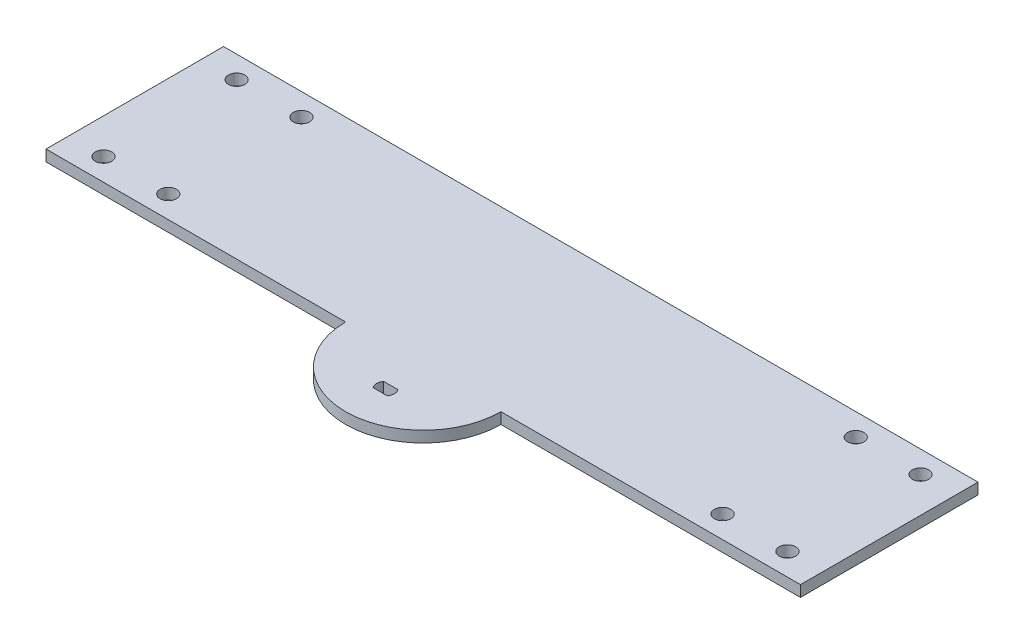
SolidWorks part; units mm, degrees
ref_plane "Front Plane" through (0, 0, 0) normal (0, 0, 1) x (1, 0, 0)
ref_plane "Top Plane" through (0, 0, 0) normal (0, 1, 0) x (1, 0, 0)
ref_plane "Right Plane" through (0, 0, 0) normal (1, 0, 0) x (0, 0, -1)
sketch "Sketch1" plane through (0, 0, 0) normal (0, 1, 0) x (1, 0, 0)
  line L0 (-2.032, 1.524) -> (2.032, 1.524)
  line L1 (-2.032, -1.524) -> (2.032, -1.524)
  line L2 (0, 0) -> (0, -11.43) construction
  line L3 (-107.95, 61.595) -> (107.95, 61.595)
  line L4 (-107.95, 61.595) -> (-107.95, 10.795)
  line L5 (-107.95, 10.795) -> (-22.225, 10.795)
  line L6 (107.95, 61.595) -> (107.95, 10.795)
  line L7 (-107.95, 61.595) -> (107.95, 10.795) construction
  line L8 (-107.95, 10.795) -> (107.95, 61.595) construction
  line L9 (22.225, 10.795) -> (107.95, 10.795)
  arc A0 (-2.032, 1.524) -> (-2.032, -1.524) centre (0, 0) ccw
  arc A1 (2.032, -1.524) -> (2.032, 1.524) centre (0, 0) ccw
  arc A2 (-22.225, 10.795) -> (22.225, 10.795) centre (0, 10.795) ccw
  point P8 (0, 36.195)
  dimension "D1" = 5.08
  dimension "D3" = 44.45
  dimension "D2" = 3.048
  dimension "D4" = 50.8
  dimension "D5" = 215.9
  dimension "D6" = 11.43
extrude "Boss-Extrude1" add sketch "Sketch1" along normal blind 3.175
sketch "Sketch2" plane through (0, 3.175, 0) normal (0, 1, 0) x (1, 0, 0)
  line L0 (-107.95, 55.245) -> (-97.8535, 55.245) construction
  line L1 (-107.95, 61.595) -> (-107.95, 10.795) construction
  line L2 (-97.8535, 10.795) -> (-97.8535, 14.7955) construction
  line L3 (107.95, 61.595) -> (-107.95, 61.595) construction
  line L4 (-107.95, 10.795) -> (-22.225, 10.795) construction
  line L6 (0, 0) -> (0, 61.595) construction
  line L9 (107.95, 55.245) -> (97.8535, 55.245) construction
  line L11 (-97.8535, 57.5945) -> (-97.8535, 61.595) construction
  circle A0 centre (-97.8535, 55.245) radius 2.3495
  circle A1 centre (-97.8535, 17.145) radius 2.3495
  circle A2 centre (-79.3115, 17.145) radius 2.3495
  circle A3 centre (-79.3115, 55.245) radius 2.3495
  circle A4 centre (79.3115, 55.245) radius 2.3495
  circle A5 centre (79.3115, 17.145) radius 2.3495
  circle A6 centre (97.8535, 17.145) radius 2.3495
  circle A7 centre (97.8535, 55.245) radius 2.3495
  point P31 (-97.8535, 14.8714)
  dimension "D3" = 4.699
  dimension "D1" = 10.0965
  dimension "D2" = 4.0005
  dimension "D4" = 18.542
extrude "Cut-Extrude1" cut sketch "Sketch2" against normal through all
